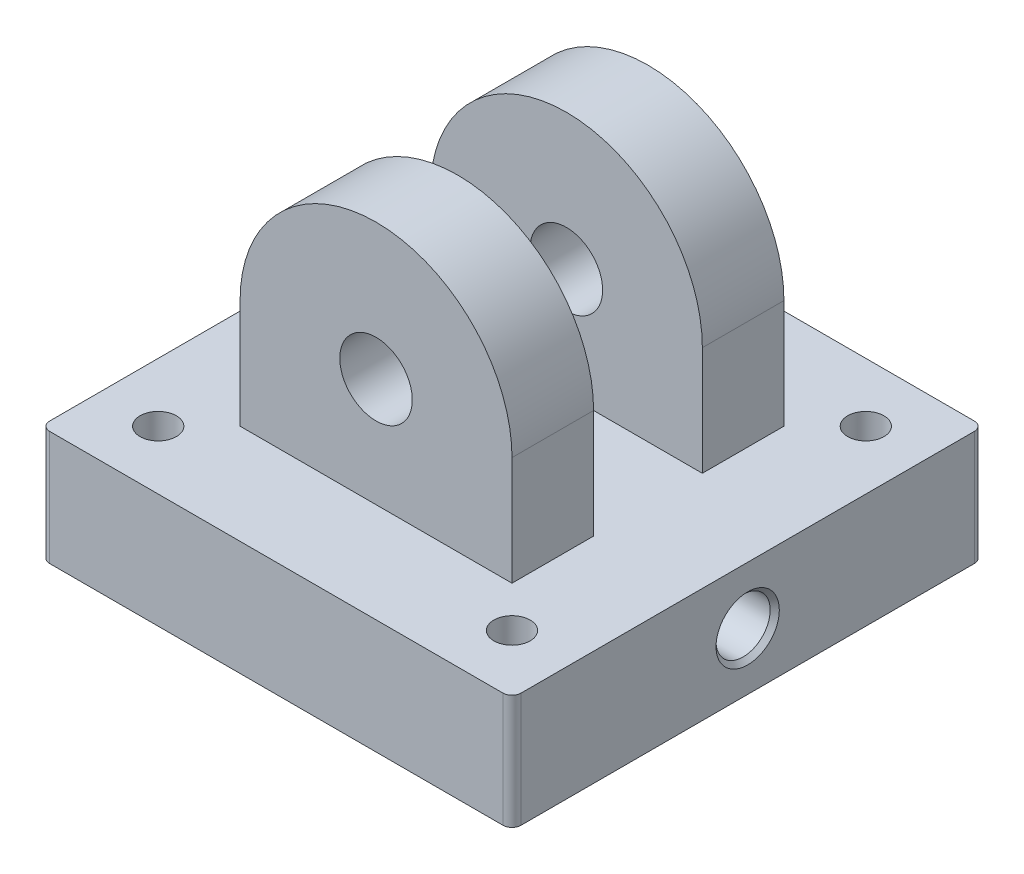
SolidWorks part; units mm, degrees
ref_plane "Front Plane" through (0, 0, 0) normal (0, 0, 1) x (1, 0, 0)
ref_plane "Top Plane" through (0, 0, 0) normal (0, 1, 0) x (1, 0, 0)
ref_plane "Right Plane" through (0, 0, 0) normal (1, 0, 0) x (0, 0, -1)
sketch "Sketch1" plane through (0, 0, 0) normal (0, 1, 0) x (1, 0, 0)
  line L9 (-82.55, -82.55) -> (82.55, -82.55)
  line L10 (-82.55, -82.55) -> (-82.55, 82.55)
  line L11 (-82.55, 82.55) -> (82.55, 82.55)
  line L12 (82.55, -82.55) -> (82.55, 82.55)
  line L13 (-82.55, -82.55) -> (82.55, 82.55) construction
  line L14 (-82.55, 82.55) -> (82.55, -82.55) construction
  point P0 (0, 0)
  dimension "D1" = 165.1
extrude "Boss-Extrude1" add sketch "Sketch1" along normal blind 38.1 and the other way blind 2
sketch "Sketch2" plane through (0, 38.1, 0) normal (0, 1, 0) x (1, 0, 0)
  line L1 (-47.625, -47.625) -> (47.625, -47.625)
  line L2 (-47.625, -47.625) -> (-47.625, 47.625)
  line L3 (-47.625, 47.625) -> (47.625, 47.625)
  line L4 (47.625, -47.625) -> (47.625, 47.625)
  line L5 (-47.625, -47.625) -> (47.625, 47.625) construction
  line L6 (-47.625, 47.625) -> (47.625, -47.625) construction
  point P0 (0, 0)
  dimension "D1" = 95.25
extrude "Boss-Extrude2" add sketch "Sketch2" along normal blind 38.1
sketch "Sketch3" plane through (0, 0, -47.625) normal (0, 0, -1) x (-1, 0, 0)
  line L0 (47.625, 76.2) -> (-47.625, 76.2)
  arc A0 (47.625, 76.2) -> (-47.625, 76.2) centre (0, 76.2) ccw
  dimension "D1" = 47.625
extrude "Boss-Extrude3" add sketch "Sketch3" against normal up to vertex
sketch "Sketch7" plane through (0, 0, -47.625) normal (0, 0, -1) x (-1, 0, 0)
  circle A0 centre (0, 76.2) radius 12.7
  dimension "D1" = 25.4
extrude "Cut-Extrude1" cut sketch "Sketch7" against normal through all
sketch "Sketch8" plane through (47.625, 0, 0) normal (1, 0, 0) x (0, 0, -1)
  line L0 (-47.625, 38.1) -> (47.625, 38.1) construction
  line L1 (-19.05, 38.1) -> (19.05, 38.1)
  line L2 (-19.05, 38.1) -> (-19.05, 1038.1)
  line L3 (-19.05, 1038.1) -> (19.05, 1038.1)
  line L4 (19.05, 38.1) -> (19.05, 1038.1)
  line L5 (-47.625, 76.2) -> (-47.625, 38.1) construction
  dimension "D1" = 38.1
  dimension "D2" = 28.575
  dimension "D3" = 1000
extrude "Cut-Extrude2" cut sketch "Sketch8" against normal through all
fillet "Fillet1" radius 3.175 4 edges at (-82.55, 18.05, 82.55) (-82.55, 18.05, -82.55) (82.55, 18.05, -82.55) (82.55, 18.05, 82.55)
sketch "Sketch9" plane through (0, -2, 0) normal (0, -1, 0) x (1, 0, 0)
  circle A0 centre (0, 0) radius 26
  dimension "D1" = 52
extrude "Cut-Extrude3" cut sketch "Sketch9" against normal blind 36.83
sketch "Sketch10" plane through (0, -2, 0) normal (0, -1, 0) x (1, 0, 0)
  circle A0 centre (0, 0) radius 69.85
  circle A1 centre (0, 0) radius 76.2
  dimension "D1" = 139.7
  dimension "D2" = 152.4
extrude "Cut-Extrude4" cut sketch "Sketch10" against normal blind 8
sketch "Sketch11" plane through (82.55, 0, 0) normal (1, 0, 0) x (0, 0, -1)
  line L0 (-79.375, 18.05) -> (79.375, 18.05) construction
  line L1 (-79.375, 38.1) -> (-79.375, -2) construction
  line L2 (79.375, -2) -> (79.375, 38.1) construction
hole_wizard "1/2-14 NPSM Tapped Hole2" positions "Sketch14" profile "Sketch15" tap size "1/2-14 NPSM" standard "ANSI Inch"
sketch "Sketch14" plane through (82.55, 0, 0) normal (1, 0, 0) x (0, 0, -1)
  line L0 (-79.375, 18.05) -> (79.375, 18.05) construction
  point P0 (0, 18.05)
sketch "Sketch15" plane through (82.55, 18.05, 0) normal (0, 1, 0) x (0, 0, -1)
  line L0 (0, 0) -> (0, 69.2003)
  line L1 (0, 69.2003) -> (9.4869, 63.5)
  line L2 (9.4869, 63.5) -> (9.4869, 1.6002)
  line L3 (9.4869, 1.6002) -> (11.0871, 0)
  line L5 (11.0871, 0) -> (0, 0)
  line L6 (-9.4869, 1.6002) -> (-11.0871, 0) construction
  line L10 (0, 69.2003) -> (-9.4869, 63.5) construction
  line L11 (0, -6.35) -> (0, 107.95) construction
  dimension "Tap Drill Dia." = 18.9738
  dimension "Tap Drill Depth" = 63.5
  dimension "Near C'Sink Dia." = 22.1742
  dimension "Near C'Sink Angle" = 90
  dimension "Drill Angle" = 118
cosmetic thread "Hole Thread2" parameters "D1"=41.91, "D2"=20.9042
sketch "Sketch16" plane through (0, -2, 0) normal (0, -1, 0) x (1, 0, 0)
  line L0 (82.55, 79.375) -> (82.55, -79.375) construction
  circle A0 centre (50.55, 0) radius 6.35
  dimension "D1" = 12.7
  dimension "D2" = 32
extrude "Cut-Extrude5" cut sketch "Sketch16" against normal blind 25
sketch "Sketch17" plane through (0, -2, 0) normal (0, -1, 0) x (1, 0, 0)
  line L1 (61.9638, -61.9638) -> (-61.9638, -61.9638) construction
  line L2 (61.9638, -61.9638) -> (61.9638, 61.9638) construction
  line L3 (61.9638, 61.9638) -> (-61.9638, 61.9638) construction
  line L4 (-61.9638, -61.9638) -> (-61.9638, 61.9638) construction
  line L5 (61.9638, -61.9638) -> (-61.9638, 61.9638) construction
  line L6 (61.9638, 61.9638) -> (-61.9638, -61.9638) construction
  circle A0 centre (0, 0) radius 87.63 construction
  circle A1 centre (-61.9638, 61.9638) radius 6.35
  circle A2 centre (61.9638, 61.9638) radius 6.35
  circle A3 centre (61.9638, -61.9638) radius 6.35
  circle A4 centre (-61.9638, -61.9638) radius 6.35
  dimension "D1" = 175.26
  dimension "D2" = 12.7
extrude "Cut-Extrude6" cut sketch "Sketch17" against normal through all
